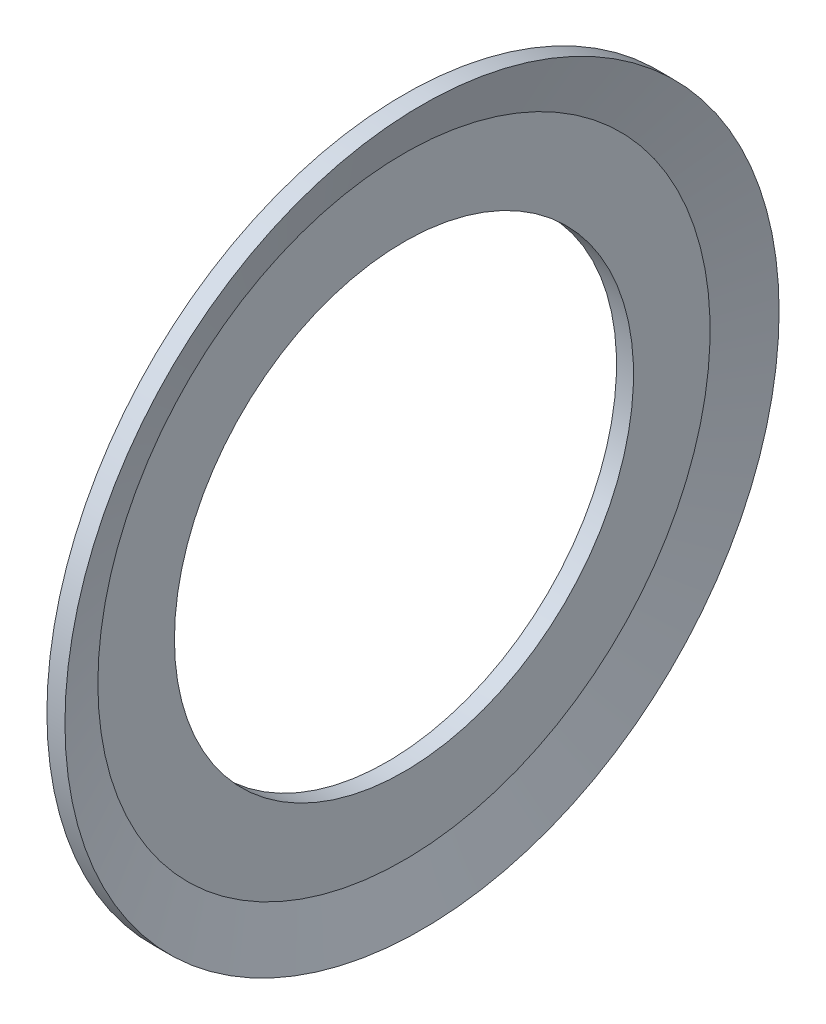
SolidWorks part; units mm, degrees
ref_plane "Plane1" through (0, 0, 0) normal (0, 0, 1) x (1, 0, 0)
ref_plane "Plane2" through (0, 0, 0) normal (0, 1, 0) x (1, 0, 0)
ref_plane "Plane3" through (0, 0, 0) normal (1, 0, 0) x (0, 0, -1)
sketch "Esquisse1" plane through (0, 0, 0) normal (0, 0, 1) x (1, 0, 0)
  line L0 (0, 13.5) -> (0, 18.175)
  line L1 (0, 18.175) -> (0.9998, 21)
  line L2 (0.9998, 21) -> (2.0606, 21)
  line L3 (2.0606, 21) -> (1, 18.0033)
  line L4 (1, 18.0033) -> (1, 13.5)
  line L5 (1, 13.5) -> (0, 13.5)
  line L6 (0, 0) -> (21.6903, 0) construction
  dimension "D1" = 13.5
  dimension "D2" = 1
  dimension "D3" = 1
  dimension "D4" = 21
  dimension "D5" = 18.175
  dimension "D6" = 19.49
revolve "Base-Révolution" add sketch "Esquisse1" angle 360 about L6
